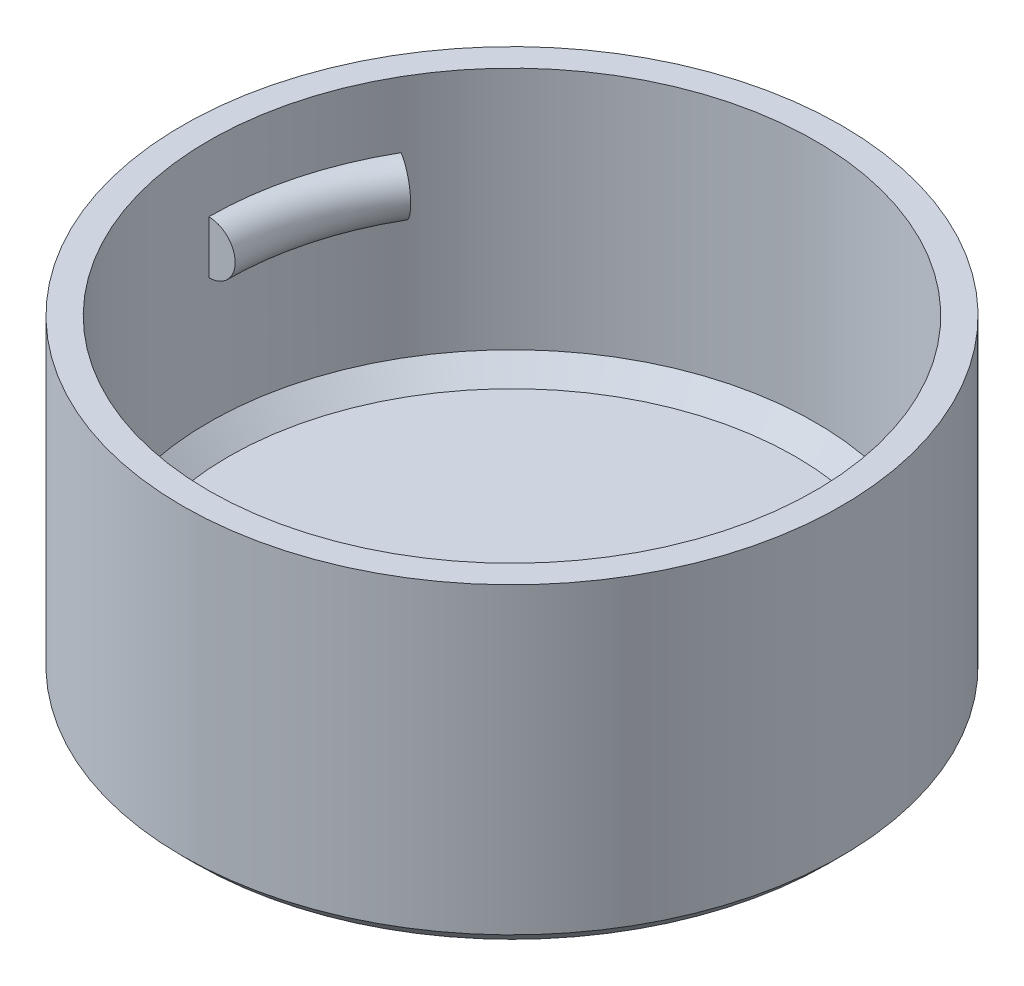
SolidWorks part; units mm, degrees
ref_plane "Front Plane" through (0, 0, 0) normal (0, 0, 1) x (1, 0, 0)
ref_plane "Top Plane" through (0, 0, 0) normal (0, 1, 0) x (1, 0, 0)
ref_plane "Right Plane" through (0, 0, 0) normal (1, 0, 0) x (0, 0, -1)
sketch "Sketch1" plane through (0, 0, 0) normal (0, 1, 0) x (1, 0, 0)
  circle A0 centre (0, 0) radius 12.5
  dimension "D1" = 25
extrude "Boss-Extrude2" add sketch "Sketch1" along normal blind 2
sketch "Sketch2" plane through (0, 2, 0) normal (0, 1, 0) x (1, 0, 0)
  circle A0 centre (0, 0) radius 11.5
  circle A1 centre (0, 0) radius 12.5
  dimension "D1" = 23
  dimension "D2" = 1
extrude "Boss-Extrude3" add sketch "Sketch2" along normal blind 10
sketch "Sketch3" plane through (0, 0, 0) normal (0, 0, 1) x (1, 0, 0)
  line L0 (-11.5, 18.2085) -> (-11.5, -5.4371) construction
  line L1 (-12.5, 0) -> (12.5, 0) construction
  line L2 (0, 19.4985) -> (0, 0) construction
  line L3 (-11.5, 9.5) -> (-11.5, 7.5)
  line L4 (11.5, 9.5) -> (11.5, 7.5)
  arc A0 (-11.5, 9.5) -> (-11.5, 7.5) centre (-11.5, 8.5) cw
  arc A1 (11.5, 9.5) -> (11.5, 7.5) centre (11.5, 8.5) ccw
  dimension "D2" = 1
  dimension "D4" = 2
  dimension "D1" = 11.5
  dimension "D3" = 8.5
revolve "Revolve1" add sketch "Sketch3" angle 30 about L2
chamfer "Chamfer1" distance 0.5 angle 45 1 edges at (0, 0, 12.5)
chamfer "Chamfer2" distance 0.75 angle 45 1 edges at (0, 2, 11.5)
